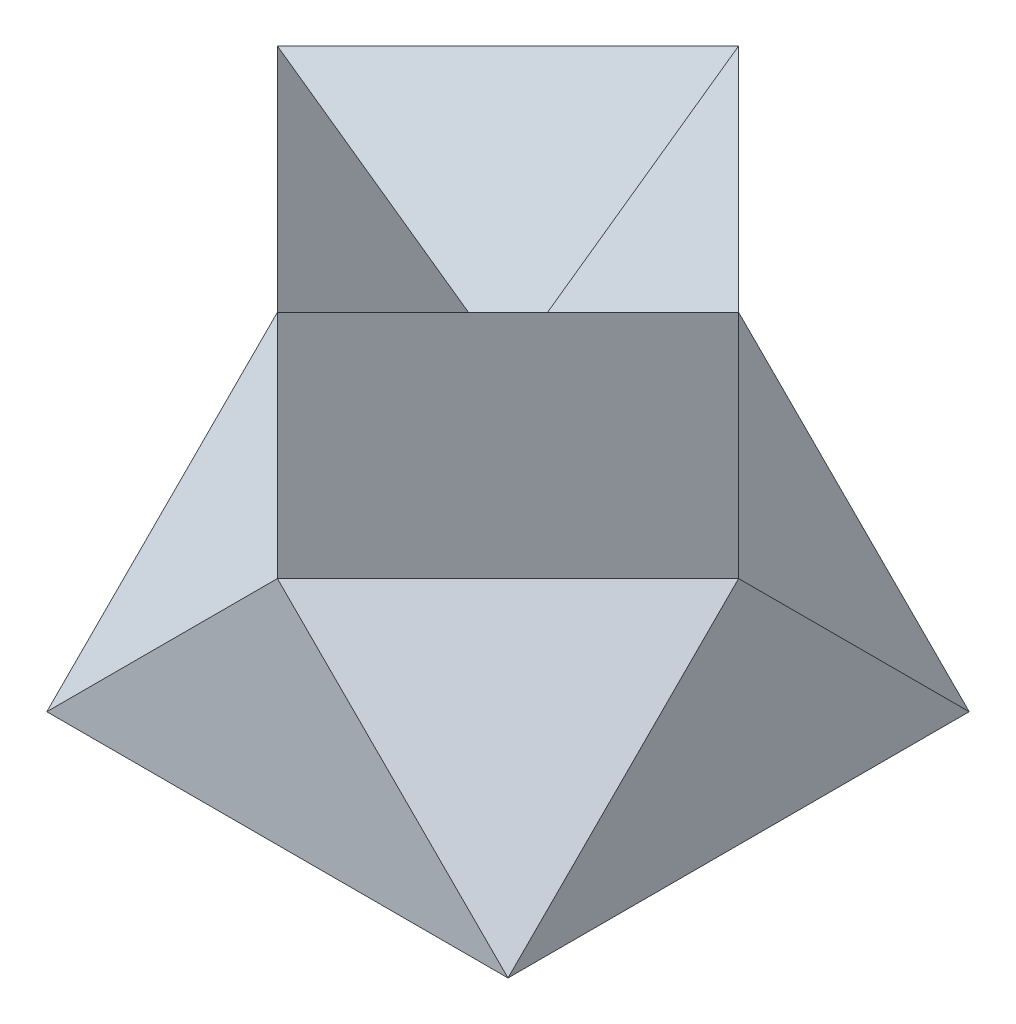
SolidWorks part; units mm, degrees
ref_plane "Front" through (0, 0, 0) normal (0, 0, 1) x (1, 0, 0)
ref_plane "Top" through (0, 0, 0) normal (0, 1, 0) x (1, 0, 0)
ref_plane "Right" through (0, 0, 0) normal (1, 0, 0) x (0, 0, -1)
sketch "Sketch1" plane through (0, 0, 0) normal (0, 1, 0) x (1, 0, 0)
  line L1 (-2, -2) -> (2, -2)
  line L2 (-2, -2) -> (-2, 2)
  line L3 (-2, 2) -> (2, 2)
  line L4 (2, -2) -> (2, 2)
  line L5 (-2, -2) -> (2, 2) construction
  line L6 (-2, 2) -> (2, -2) construction
  point P0 (0, 0)
  dimension "D1" = 4
  dimension "D2" = 4
extrude "Boss-Extrude1" add sketch "Sketch1" along normal blind 4
sketch "Sketch2" plane through (0, 4, 0) normal (0, 1, 0) x (1, 0, 0)
  line L0 (-2, 0) -> (0, -2)
  line L1 (-2, 0) -> (0, 2)
  line L2 (0, -2) -> (2, 0)
  line L3 (0, 2) -> (2, 0)
  line L4 (-2, 2) -> (-2, -2) construction
  line L5 (-2, -2) -> (2, -2) construction
  dimension "D1" = 2
extrude "Cut-Extrude1" cut sketch "Sketch2" against normal blind 3 draft 45
sketch3d "3DSketch1"
  line L0 (0, 4, 2) -> (0, 2, 2)
  line L1 (0, 2, 2) -> (-2, 2, 0)
  line L2 (-2, 2, 0) -> (-2, 4, 0)
  line L3 (-2, 4, 0) -> (-2, 4, 2) construction
  line L4 (-2, 4, 0) -> (0, 4, 2)
  line L5 (-2, 4, -2) -> (-2, 4, 0) construction
  point P7 (-2, 2.8564, 0.4779)
  point P8 (-2, 4, 0)
  dimension "D1" = 0
  dimension "D2" = 2
  dimension "D3" = 2
  dimension "D4" = 2
extrude "Cut-Extrude2" cut sketch "3DSketch1" along direction (0, 0, -1) on the side against the normal blind 3
mirror "Mirror1" about plane through (0, 0, 0) normal (1, 0, 0) of "Cut-Extrude2"
mirror "Mirror2" about plane through (0, 0, 0) normal (0, 0, 1) of "Mirror1", "Cut-Extrude2"
sketch3d "3DSketch2"
  line L0 (-2, 2, 0) -> (-2, 0, 2)
  line L1 (-2, 0, 2) -> (0, 2, 2)
  line L2 (0, 2, 2) -> (-2, 2, 0)
extrude "Cut-Extrude3" cut sketch "3DSketch2" along direction (1, 0, 0) on the side against the normal blind 3
mirror "Mirror3" about plane through (0, 0, 0) normal (1, 0, 0) of "Cut-Extrude3"
mirror "Mirror4" about plane through (0, 0, 0) normal (0, 0, 1) of "Mirror3", "Cut-Extrude3"
